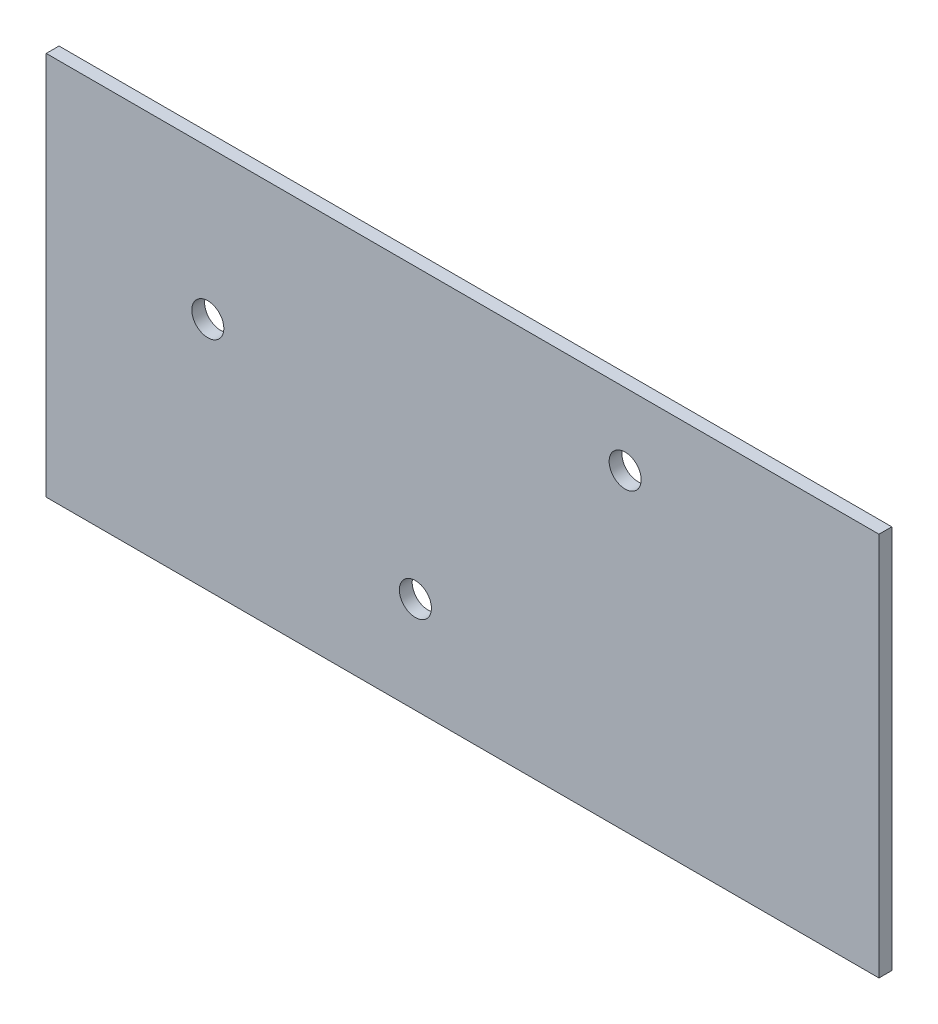
SolidWorks part; units mm, degrees
ref_plane "Front Plane" through (0, 0, 0) normal (0, 0, 1) x (1, 0, 0)
ref_plane "Top Plane" through (0, 0, 0) normal (0, 1, 0) x (1, 0, 0)
ref_plane "Right Plane" through (0, 0, 0) normal (1, 0, 0) x (0, 0, -1)
sketch "Sketch1" plane through (0, 0, 0) normal (0, 0, 1) x (1, 0, 0)
  line L1 (-82.55, -38.1) -> (82.55, -38.1)
  line L2 (-82.55, -38.1) -> (-82.55, 38.1)
  line L3 (-82.55, 38.1) -> (82.55, 38.1)
  line L4 (82.55, -38.1) -> (82.55, 38.1)
  point P4 (0, 38.1)
  point P6 (-82.55, 0)
  point P7 (-367.1455, 75.9691)
  dimension "D1" = 76.2
  dimension "D2" = 165.1
extrude "Boss-Extrude1" add sketch "Sketch1" along normal blind 2.54
hole_wizard "1/4 (0.2500) Dowel Hole1" positions "3DSketch1" profile "Sketch2" hole size "1/4" standard "ANSI Inch" end condition through all
sketch3d "3DSketch1"
  point P0 (-50.5126, 8.4748, 2.54)
  point P2 (-9.3577, -18.9893, 2.54)
  point P4 (32.2273, 23.8611, 2.54)
  point P8 (-9.3577, -18.9893, 2.54)
sketch "Sketch2" plane through (-50.5126, 8.4748, 2.54) normal (1, 0, 0) x (0, -1, 0)
  line L0 (0, 0) -> (0, 2.54)
  line L1 (0, 2.54) -> (3.175, 2.54)
  line L2 (3.175, 2.54) -> (3.175, 0)
  line L5 (3.175, 0) -> (0, 0)
  line L11 (0, -6.35) -> (0, 107.95) construction
  dimension "Thru Hole Dia." = 6.35
  dimension "Thru Hole Depth" = 2.54
